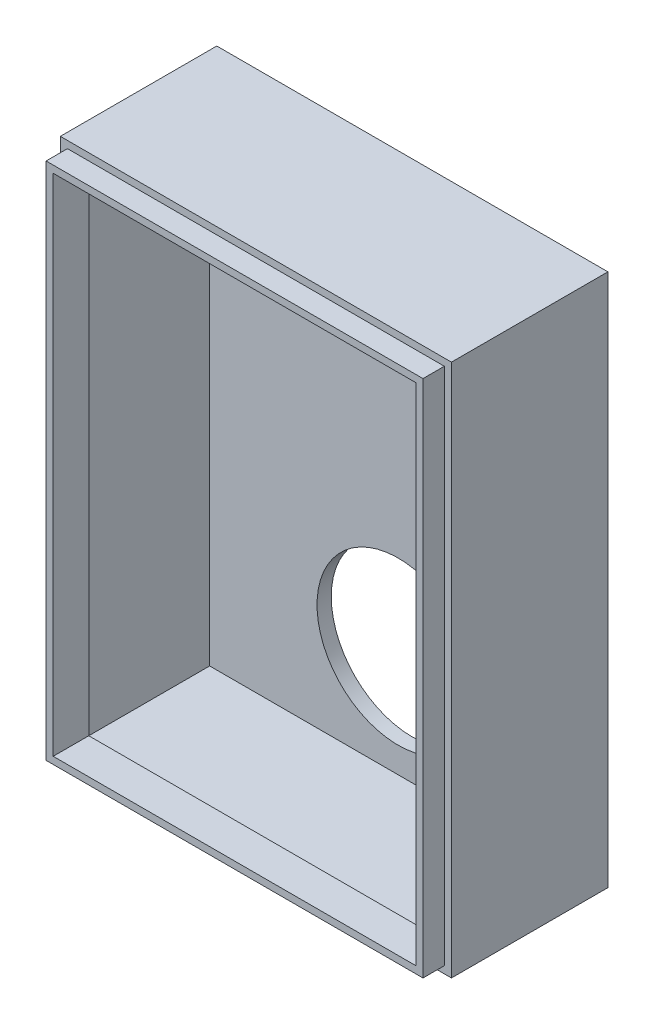
SolidWorks part; units mm, degrees
material "PA Тип 6"
ref_plane "Спереди" through (0, 0, 0) normal (0, 0, 1) x (1, 0, 0)
ref_plane "Сверху" through (0, 0, 0) normal (0, 1, 0) x (1, 0, 0)
ref_plane "Справа" through (0, 0, 0) normal (1, 0, 0) x (0, 0, -1)
sketch "Эскиз1" plane through (0, 0, 0) normal (0, 0, 1) x (1, 0, 0)
  line L1 (0, 0) -> (55, 0)
  line L2 (0, 0) -> (0, 75)
  line L3 (0, 75) -> (55, 75)
  line L4 (55, 0) -> (55, 75)
  dimension "D1" = 55
  dimension "D2" = 75
extrude "Бобышка-Вытянуть1" add sketch "Эскиз1" along normal blind 2
sketch "Эскиз2" plane through (0, 0, 2) normal (0, 0, 1) x (1, 0, 0)
  line L1 (0, 75) -> (55, 75)
  line L2 (0, 75) -> (0, 0)
  line L3 (0, 0) -> (55, 0)
  line L4 (55, 75) -> (55, 0)
  line L5 (1, 74) -> (54, 74)
  line L6 (1, 74) -> (1, 1)
  line L7 (1, 1) -> (54, 1)
  line L8 (54, 74) -> (54, 1)
  dimension "D1" = 1
  dimension "D2" = 1
  dimension "D3" = 1
  dimension "D4" = 1
extrude "Бобышка-Вытянуть2" add sketch "Эскиз2" along normal blind 20
sketch "Эскиз3" plane through (0, 0, 22) normal (0, 0, 1) x (1, 0, 0)
  line L0 (1, 74) -> (1, 1) construction
  line L1 (1, 74) -> (54, 74)
  line L2 (1, 74) -> (1, 1)
  line L3 (1, 1) -> (54, 1)
  line L4 (54, 74) -> (54, 1)
  line L6 (2, 73) -> (53, 73)
  line L7 (2, 73) -> (2, 2)
  line L8 (2, 2) -> (53, 2)
  line L9 (53, 73) -> (53, 2)
  dimension "D1" = 1
  dimension "D2" = 1
  dimension "D3" = 1
  dimension "D4" = 1
extrude "Бобышка-Вытянуть3" add sketch "Эскиз3" along normal blind 3 and the other way blind 2 separate body
sketch "Эскиз4" plane through (0, 0, 2) normal (0, 0, 1) x (1, 0, 0)
  line L1 (55, 0) -> (55, 75) construction
  line L3 (1, 1) -> (54, 1) construction
  circle A0 centre (27.5, 16) radius 11.4
  circle A1 centre (27.5, 63) radius 4
  dimension "D1" = 22.8
  dimension "D2" = 15
  dimension "D3" = 27.5
  dimension "D4" = 47
  dimension "D5" = 8
  dimension "D6" = 27.5
extrude "Вырез-Вытянуть1" cut sketch "Эскиз4" against normal blind 3
